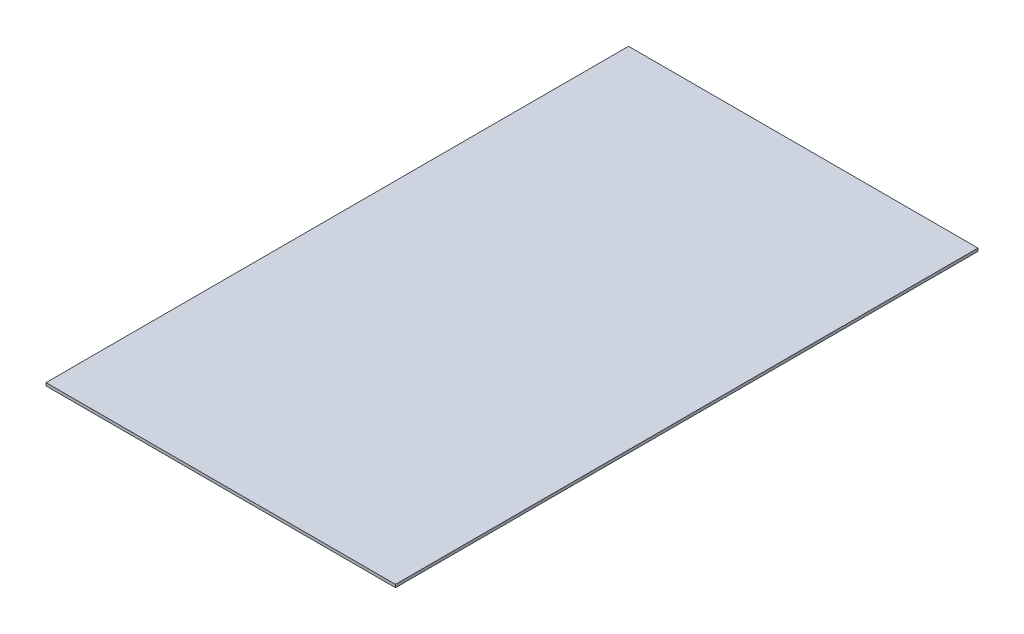
SolidWorks part; units mm, degrees
ref_plane "Front Plane" through (0, 0, 0) normal (0, 0, 1) x (1, 0, 0)
ref_plane "Top Plane" through (0, 0, 0) normal (0, 1, 0) x (1, 0, 0)
ref_plane "Right Plane" through (0, 0, 0) normal (1, 0, 0) x (0, 0, -1)
sketch "Sketch1" plane through (0, 0, 0) normal (0, 1, 0) x (1, 0, 0)
  line L1 (-60, -100) -> (60, -100)
  line L2 (-60, -100) -> (-60, 100)
  line L3 (-60, 100) -> (60, 100)
  line L4 (60, -100) -> (60, 100)
  line L5 (-60, -100) -> (60, 100) construction
  line L6 (-60, 100) -> (60, -100) construction
  point P0 (0, 0)
  dimension "D1" = 200
  dimension "D2" = 120
extrude "Boss-Extrude1" add sketch "Sketch1" along normal blind 1
